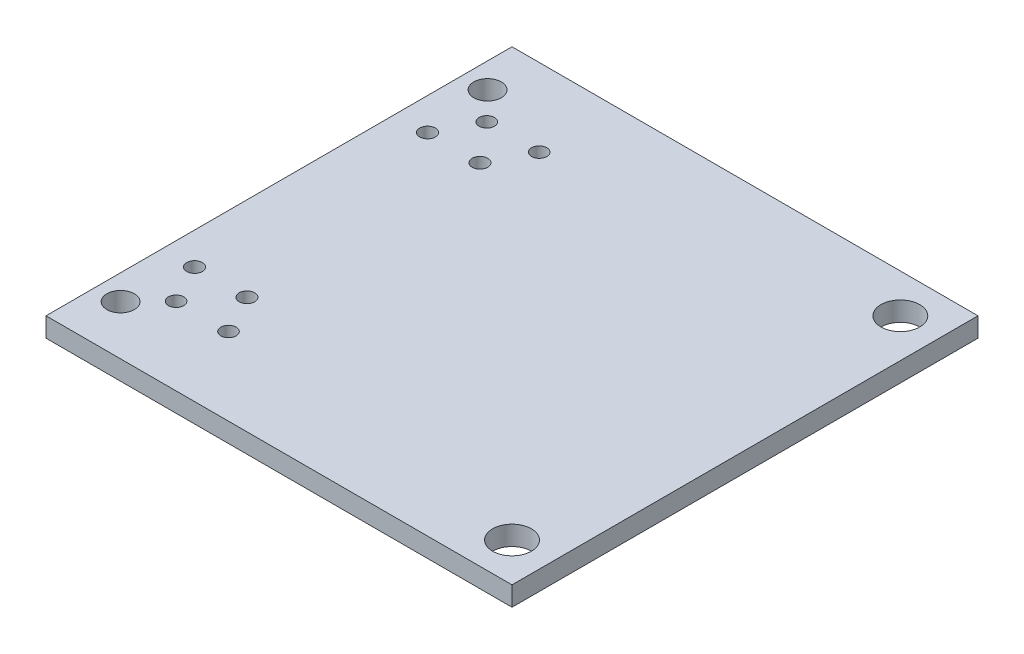
SolidWorks part; units mm, degrees
ref_plane "Front Plane" through (0, 0, 0) normal (0, 0, 1) x (1, 0, 0)
ref_plane "Top Plane" through (0, 0, 0) normal (0, 1, 0) x (1, 0, 0)
ref_plane "Right Plane" through (0, 0, 0) normal (1, 0, 0) x (0, 0, -1)
sketch "Sketch1" plane through (0, 0, 0) normal (0, 1, 0) x (1, 0, 0)
  line L1 (0, 0) -> (152.4, 0)
  line L2 (0, 0) -> (0, 152.4)
  line L3 (0, 152.4) -> (152.4, 152.4)
  line L4 (152.4, 0) -> (152.4, 152.4)
  circle A0 centre (8.2, 136.1999) radius 4.5
  circle A1 centre (8.2, 16.2) radius 4.5
  circle A2 centre (17.145, 25.4) radius 2.5
  circle A3 centre (34.29, 25.4) radius 2.5
  circle A4 centre (17.145, 127) radius 2.5
  circle A5 centre (34.29, 127) radius 2.5
  circle A6 centre (139.7, 12.7) radius 6.35
  circle A7 centre (139.7, 139.7) radius 6.35
  dimension "D9" = 9
  dimension "D10" = 5
  dimension "D16" = 12.7
  dimension "D1" = 152.4
  dimension "D2" = 152.4
  dimension "D3" = 8.2
  dimension "D5" = 136.1999
  dimension "D6" = 16.2
  dimension "D7" = 17.145
  dimension "D8" = 34.29
  dimension "D11" = 25.4
  dimension "D12" = 25.4
  dimension "D13" = 12.7
  dimension "D14" = 12.7
  dimension "D15" = 12.7
extrude "Boss-Extrude1" add sketch "Sketch1" along normal blind 6.35
sketch "Sketch2" plane through (0, 6.35, 0) normal (0, 1, 0) x (1, 0, 0)
  line L0 (38.1, 152.4) -> (38.1, 0) construction
  line L1 (152.4, 152.4) -> (0, 152.4) construction
  line L2 (0, 0) -> (152.4, 0) construction
  line L3 (0, 114.3) -> (10.4775, 114.3) construction
  line L4 (0, 152.4) -> (0, 0) construction
  line L5 (10.4775, 114.3) -> (27.6225, 114.3) construction
  line L6 (27.6225, 114.3) -> (38.1, 114.3) construction
  line L7 (0, 38.1) -> (10.4775, 38.1) construction
  line L8 (10.4775, 38.1) -> (27.6225, 38.1) construction
  line L9 (27.6225, 38.1) -> (38.1, 38.1) construction
  line L10 (10.4775, 152.4) -> (10.4775, 114.3) construction
  line L12 (10.4775, 38.1) -> (10.4775, 0) construction
  circle A0 centre (10.4775, 114.3) radius 2.5527
  circle A1 centre (27.6225, 114.3) radius 2.5527
  circle A2 centre (10.4775, 38.1) radius 2.5527
  circle A3 centre (27.6225, 38.1) radius 2.5527
  dimension "D3" = 5.1054
  dimension "D1" = 38.1
  dimension "D2" = 17.145
  dimension "D4" = 38.1
extrude "Cut-Extrude1" cut sketch "Sketch2" against normal blind 6.35
